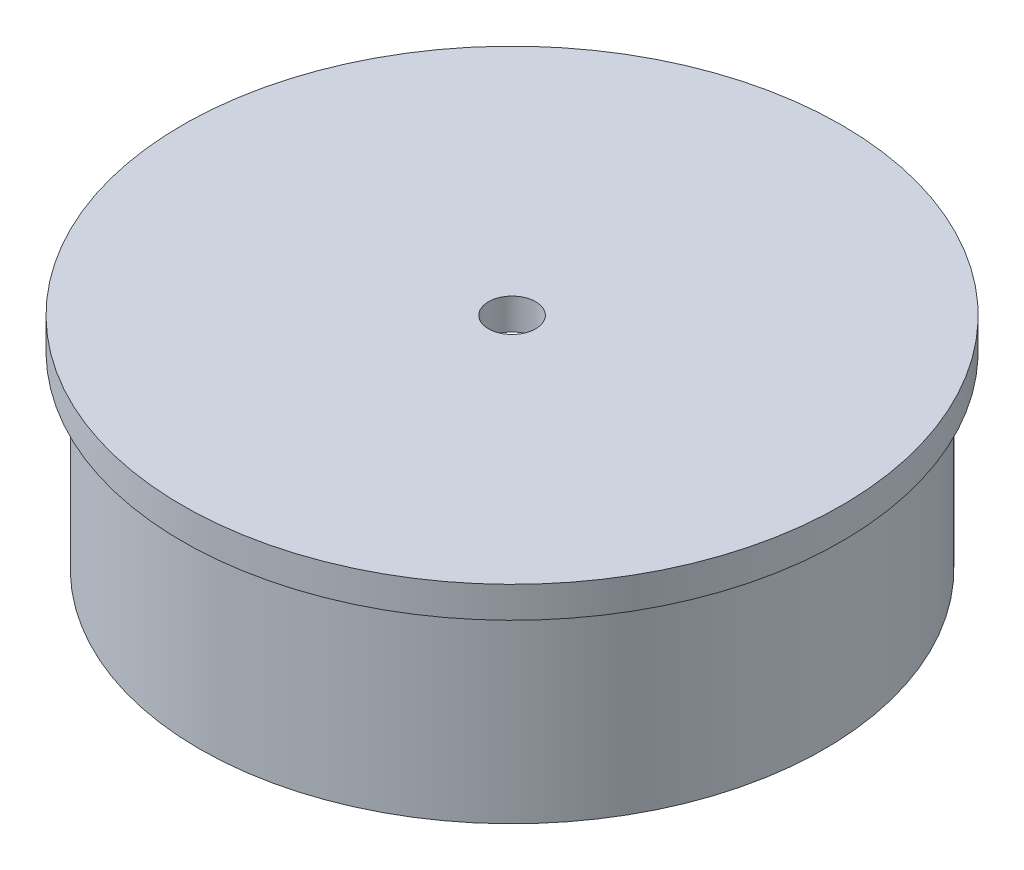
SolidWorks part; units mm, degrees
ref_plane "Front Plane" through (0, 0, 0) normal (0, 0, 1) x (1, 0, 0)
ref_plane "Top Plane" through (0, 0, 0) normal (0, 1, 0) x (1, 0, 0)
ref_plane "Right Plane" through (0, 0, 0) normal (1, 0, 0) x (0, 0, -1)
sketch "Sketch1" plane through (0, 0, 0) normal (0, 0, 1) x (1, 0, 0)
  line L0 (0, 0) -> (0, 67.0575) construction
  line L1 (-21.0693, -14.8) -> (-21.0693, -2.1)
  line L2 (-21.0693, -2.1) -> (-22.225, -2.1)
  line L3 (-22.225, -2.1) -> (-22.225, 0)
  line L4 (-22.225, 0) -> (-1.5875, 0)
  line L5 (-1.5875, 0) -> (-1.5875, -2.1)
  line L6 (-1.5875, -2.1) -> (-17.4879, -2.1)
  line L7 (-20.0279, -4.64) -> (-20.0279, -14.8)
  line L8 (-20.0279, -14.8) -> (-21.0693, -14.8)
  arc A0 (-17.4879, -2.1) -> (-20.0279, -4.64) centre (-17.4879, -4.64) ccw
  dimension "D4" = 2.54
  dimension "D1" = 44.45
  dimension "D2" = 42.1386
  dimension "D3" = 3.175
  dimension "D5" = 12.7
  dimension "D6" = 1.0414
  dimension "D7" = 2.1
revolve "Revolve1" add sketch "Sketch1" angle 360 mid plane about L0
ref_plane "Plane1" through (0, 0, -9.525) normal (0, 0, 1) x (1, 0, 0)
sketch "Sketch2" plane through (0, 0, -9.525) normal (0, 0, 1) x (1, 0, 0)
  line L0 (-1.5875, -2.1) -> (-1.5875, -4.5552)
  line L1 (-17.4879, -2.1) -> (17.4879, -2.1) construction
  line L2 (1.5875, -4.5552) -> (1.5875, -2.1)
  line L3 (-22.225, -2.1) -> (22.225, -2.1) construction
  arc A0 (-1.5875, -4.5552) -> (1.5875, -4.5552) centre (0, -4.5552) ccw
  dimension "D1" = 1.5875
sketch "Sketch3" plane through (0, -2.1, 0) normal (0, -1, 0) x (1, 0, 0)
  line L0 (1.5875, -9.525) -> (-1.5875, -9.525) construction
  line L1 (8.14, -9.525) -> (-8.14, -9.525) construction
  circle A0 centre (4.7027, -9.525) radius 2.3813
  dimension "D1" = 4.7625
sweep "Sweep1" add profiles "Sketch3" path "Sketch2"
fillet "Fillet1" radius 1.27 2 edges at (-4.7027, -2.1, -11.9062) (4.7027, -2.1, -11.9062)
mirror "Mirror1" about plane through (0, 0, 0) normal (0, 0, 1) of "Sweep1"
